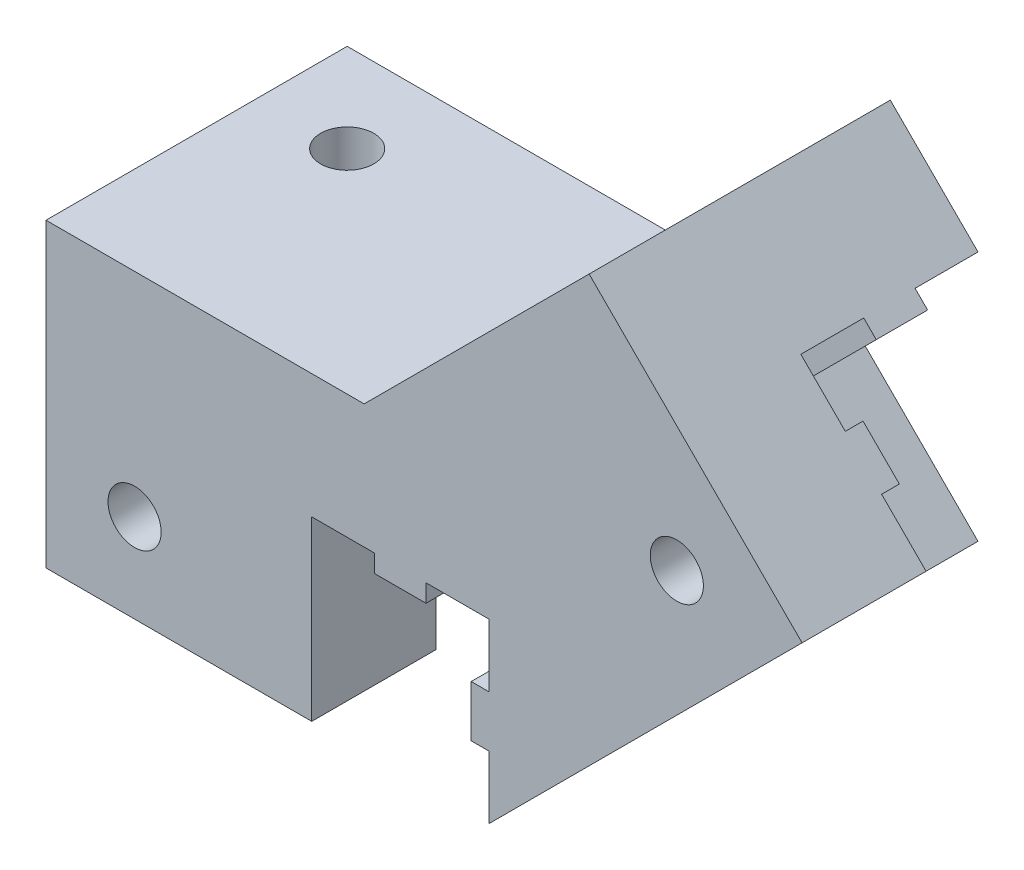
SolidWorks part; units mm, degrees
ref_plane "Front Plane" through (0, 0, 0) normal (0, 0, 1) x (1, 0, 0)
ref_plane "Top Plane" through (0, 0, 0) normal (0, 1, 0) x (1, 0, 0)
ref_plane "Right Plane" through (0, 0, 0) normal (1, 0, 0) x (0, 0, -1)
ref_plane "FrontPlane+10mm" through (0, 0, 10) normal (0, 0, 1) x (1, 0, 0)
sketch "Sketch1" plane through (0, 0, 0) normal (0, 0, 1) x (1, 0, 0)
  line L0 (-290, 0) -> (-10, 0) construction
  line L1 (0, 0) -> (-90, -90) construction
  line L2 (-10, 0) -> (0, 0) construction
  line L3 (-10, 0) -> (-10, 10) construction
  line L4 (-10, 10) -> (0, 10) construction
  line L5 (0, 0) -> (0, 10) construction
  line L6 (-90, -90) -> (-210, -90) construction
  line L7 (-300, 10) -> (-290, 10) construction
  line L8 (-300, 10) -> (-300, 0) construction
  line L9 (-90, -90) -> (-72.3223, -72.3223)
  line L10 (-290, 10) -> (-290, 0) construction
  line L11 (-210, -90) -> (-300, 0) construction
  line L12 (-88.1335, -73.9914) -> (-16.0086, -1.8665) construction
  line L13 (-115, -80) -> (-90, -80) construction
  line L14 (-115, -80) -> (-115, -90) construction
  line L15 (-90, -90) -> (-90, -80)
  line L16 (-90, -80) -> (-90, -90) construction
  line L17 (-16.0086, -1.8665) -> (-8.9376, -8.9376) construction
  line L18 (-88.1335, -73.9914) -> (-81.0624, -81.0624) construction
  line L19 (-16.0086, -1.8665) -> (0, 0) construction
  line L20 (-88.1335, -73.9914) -> (-90, -90) construction
  line L21 (-90, -80) -> (-115, -80)
  line L22 (-115, -80) -> (-115, -73)
  line L23 (-115, -73) -> (-97.0416, -73)
  line L24 (-97.0416, -73) -> (-84.3431, -60.3015)
  line L25 (-84.3431, -60.3015) -> (-72.3223, -72.3223)
  dimension "D1" = 10
  dimension "D2" = 10
  dimension "D3" = 300
  dimension "D4" = 10
  dimension "D5" = 120
  dimension "D6" = 135
  dimension "D7" = 45
  dimension "D8" = 45
  dimension "D9" = 127.2792
  dimension "D10" = 7
  dimension "D11" = 10
  dimension "D12" = 10
  dimension "D13" = 102
  dimension "D14" = 25
  dimension "D15" = 7
  dimension "D16" = 25
  dimension "D17" = 90
extrude "Main" add sketch "Sketch1" along normal blind 17
sketch "Sketch2" plane through (-72.3223, -72.3223, 0) normal (0.7071, 0.7071, 0) x (0.7071, -0.7071, 0)
  line L0 (-3.55, -10) -> (0, -10)
  line L1 (-10, -3.55) -> (-9, -3.55)
  line L2 (-9, -3.55) -> (-9, -6.45)
  line L3 (-9, -6.45) -> (-10, -6.45)
  line L4 (-6.45, -10) -> (-10, -10)
  line L5 (0, 0) -> (-17, 0) construction
  line L6 (-10, 0) -> (0, 0)
  line L7 (0, 0) -> (0, -10)
  line L8 (0, -17) -> (0, 0) construction
  line L10 (-6.45, -10) -> (-6.45, -9)
  line L11 (-6.45, -9) -> (-3.55, -9)
  line L12 (-3.55, -9) -> (-3.55, -10)
  line L13 (-10, -10) -> (-10, -6.45)
  line L15 (-10, -3.55) -> (-10, 0)
  dimension "D1" = 10
  dimension "D2" = 2.9
  dimension "D3" = 3.55
  dimension "D4" = 1
  dimension "D5" = 10
extrude "Cut-Extrude1" cut sketch "Sketch2" against normal blind 10
sketch "Sketch3" plane through (0, 0, 17) normal (0, 0, 1) x (1, 0, 0)
  line L0 (-90, -90) -> (-72.3223, -72.3223) construction
  line L1 (-72.3223, -72.3223) -> (-84.3431, -60.3015) construction
  circle A0 centre (-79.3934, -72.3223) radius 1.5
  dimension "D1" = 3
  dimension "D2" = 5
  dimension "D3" = 5
extrude "Cut-Extrude2" cut sketch "Sketch3" against normal through all
sketch "Sketch4" plane through (0, 0, 10) normal (0, 0, 1) x (1, 0, 0)
  line L0 (-96.45, -80) -> (-96.45, -81)
  line L1 (-115, -80) -> (-90, -80) construction
  line L2 (-96.45, -81) -> (-93.55, -81)
  line L3 (-93.55, -81) -> (-93.55, -80)
  line L4 (-93.55, -80) -> (-96.45, -80)
  line L6 (-90, -80) -> (-90, -90) construction
  line L7 (-90, -86.45) -> (-91, -86.45)
  line L8 (-90, -86.45) -> (-90, -83.55)
  line L9 (-90, -83.55) -> (-91, -83.55)
  line L10 (-91, -86.45) -> (-91, -83.55)
  dimension "D1" = 3.55
  dimension "D2" = 1
  dimension "D3" = 2.9
  dimension "D4" = 3.55
extrude "Boss-Extrude1" add sketch "Sketch4" along normal up to surface (7 mm away) up to face at (-77.8934, -72.3223, 17)
sketch "Sketch5" plane through (0, -80, 0) normal (0, -1, 0) x (1, 0, 0)
  line L0 (-115, 17) -> (-115, 0) construction
  line L1 (-115, 6.45) -> (-100, 6.45)
  line L2 (-115, 6.45) -> (-115, 3.55)
  line L3 (-115, 3.55) -> (-100, 3.55)
  line L4 (-100, 6.45) -> (-100, 3.55)
  line L5 (-115, 0) -> (-90, 0) construction
  dimension "D1" = 2.9
  dimension "D2" = 3.55
  dimension "D3" = 15
extrude "Boss-Extrude2" add sketch "Sketch5" along normal blind 1
sketch "Sketch6" plane through (0, -73, 0) normal (0, 1, 0) x (1, 0, 0)
  line L0 (-115, -17) -> (-115, 0) construction
  line L3 (-97.0416, 0) -> (-115, 0) construction
  circle A0 centre (-110, -5) radius 1.5
  dimension "D1" = 3
  dimension "D2" = 5
  dimension "D3" = 5
extrude "Cut-Extrude3" cut sketch "Sketch6" against normal through all
sketch "Sketch7" plane through (-115, 0, 0) normal (-1, 0, 0) x (0, 0, 1)
  line L0 (17, -80) -> (17, -90)
  line L1 (17, -90) -> (10, -90)
  line L2 (10, -90) -> (10, -86.45)
  line L3 (10, -86.45) -> (9, -86.45)
  line L4 (9, -86.45) -> (9, -83.55)
  line L5 (9, -83.55) -> (10, -83.55)
  line L6 (10, -83.55) -> (10, -80)
  line L7 (17, -80) -> (6.45, -80) construction
  line L8 (10, -80) -> (17, -80)
  line L9 (10, -79.3934) -> (10, -72.3223) construction
  dimension "D1" = 2.9
  dimension "D2" = 1
extrude "Boss-Extrude3" add sketch "Sketch7" against normal blind 15
sketch "Sketch8" plane through (0, 0, 17) normal (0, 0, 1) x (1, 0, 0)
  line L0 (-100, -90) -> (-115, -90) construction
  line L3 (-115, -73) -> (-115, -90) construction
  circle A0 centre (-110, -85) radius 1.5
  dimension "D1" = 3
  dimension "D2" = 5
  dimension "D3" = 5
extrude "Cut-Extrude4" cut sketch "Sketch8" against normal through all
sketch "Sketch9" plane through (-90, 0, 0) normal (-1, 0, 0) x (0, 0, 1)
  line L0 (0, -80) -> (0, -90) construction
  line L1 (17, -90) -> (0, -90) construction
  circle A0 centre (5, -85) radius 1.5
  dimension "D1" = 3
  dimension "D2" = 5
  dimension "D3" = 5
extrude "Cut-Extrude5" cut sketch "Sketch9" against normal through all
ref_plane "Plane2" through (0, -55, 0) normal (0, 1, 0) x (1, 0, 0)
mirror "Mirror2" [suppressed] about plane through (0, -55, 0) normal (0, 1, 0)
sketch "Sketch10" plane through (0, 0, 17) normal (0, 0, 1) x (1, 0, 0)
  line L1 (-129.0329, -56.9977) -> (-60.2872, -56.9977)
  line L2 (-129.0329, -56.9977) -> (-129.0329, -95.4249)
  line L3 (-129.0329, -95.4249) -> (-60.2872, -95.4249)
  line L4 (-60.2872, -56.9977) -> (-60.2872, -95.4249)
extrude "Cut-Extrude6" [suppressed] cut sketch "Sketch10" against normal through all
